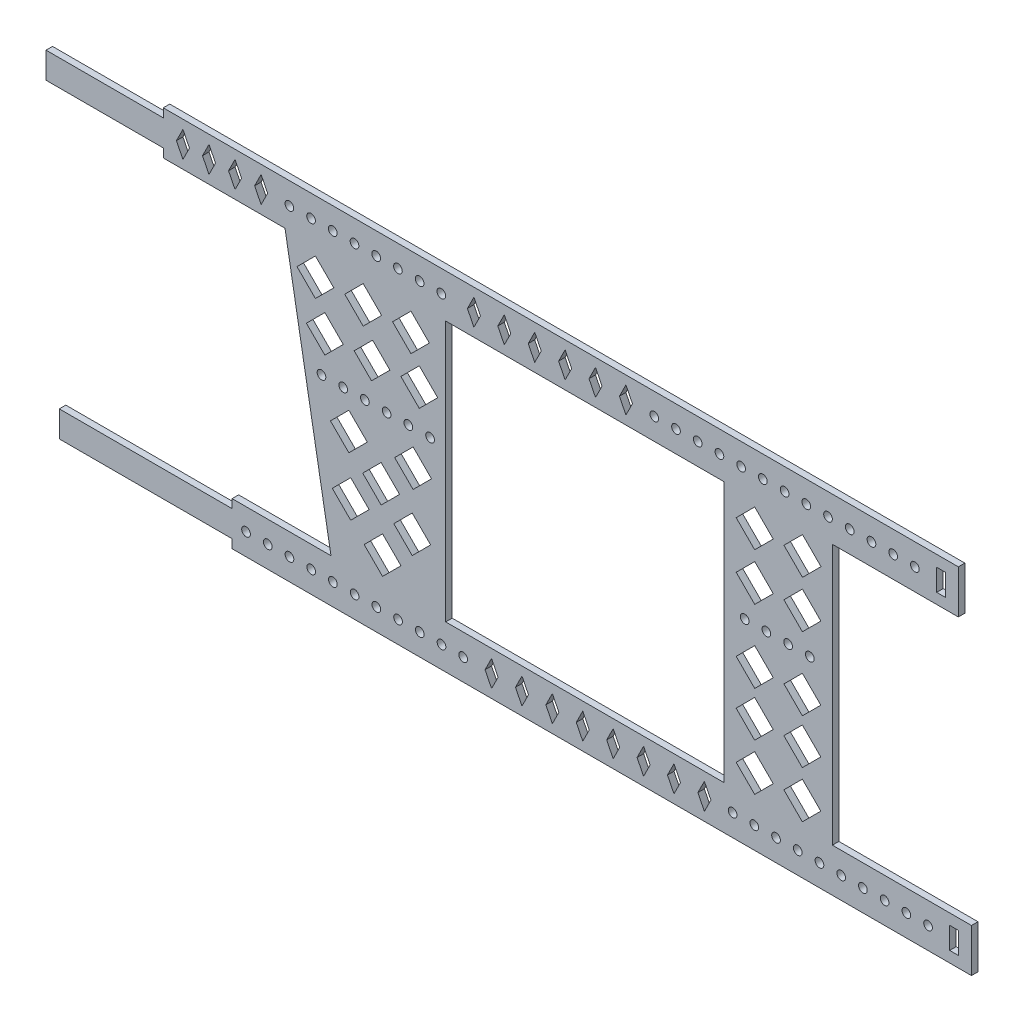
SolidWorks part; units mm, degrees
ref_plane "前视基准面" through (0, 0, 0) normal (0, 0, 1) x (1, 0, 0)
ref_plane "上视基准面" through (0, 0, 0) normal (0, 1, 0) x (1, 0, 0)
ref_plane "右视基准面" through (0, 0, 0) normal (1, 0, 0) x (0, 0, -1)
other "Configuration Table"
sketch "草图1" plane through (0, 0, 0) normal (0, 0, 1) x (1, 0, 0)
  line L4 (-82, 0.0001) -> (-80.5, 3.0002)
  line L11 (0, 0) -> (121.948, 0) construction
  line L17 (-82, 0.0001) -> (-80.4999, -3.0001)
  line L18 (-80.5, 3.0002) -> (-78.9999, 0)
  line L44 (-80.4999, -3.0001) -> (-78.9999, 0)
  line L49 (-76, 0.0001) -> (-74.5, 3.0002)
  line L51 (-91.0305, 5.0353) -> (88.0306, 5.0353)
  line L53 (-91.0305, -4.9647) -> (-62.9999, -4.9647)
  line L66 (-85, 0.0003) -> (-85, -0.0003)
  line L72 (-76, 0.0001) -> (-74.4999, -3.0001)
  line L73 (-62.9999, -4.9647) -> (-52.4203, -64.9647)
  line L74 (63.0306, -4.9647) -> (88.0306, -4.9647)
  line L75 (-25.9999, -4.9647) -> (-25.9999, -64.9647)
  line L77 (-74.4999, -3.0001) -> (-72.9999, 0)
  line L78 (-74.5, 3.0002) -> (-72.9999, 0)
  line L79 (-70, 0.0001) -> (-68.5, 3.0002)
  line L80 (-70, 0.0001) -> (-68.4999, -3.0001)
  line L81 (-68.4999, -3.0001) -> (-66.9999, 0)
  line L82 (-68.5, 3.0002) -> (-66.9999, 0)
  line L83 (-61.9999, 0) -> (-56.9999, 0) construction
  line L84 (-62.9999, 0) -> (-62.9999, -4.9647) construction
  line L85 (-25.9999, 0) -> (-25.9999, -8.8507) construction
  line L86 (-21, 0.04) -> (-19.5, 3.04)
  line L87 (-21, 0.04) -> (-19.5, -2.96)
  line L88 (-19.5, -2.96) -> (-18, 0.04)
  line L89 (-19.5, 3.04) -> (-18, 0.04)
  line L90 (-14, 0.04) -> (-12.5, 3.04)
  line L91 (-12.5, 3.04) -> (-11, 0.04)
  line L92 (-12.5, -2.96) -> (-11, 0.04)
  line L93 (-14, 0.04) -> (-12.5, -2.96)
  line L94 (-7, 0.04) -> (-5.5, 3.04)
  line L95 (-5.5, 3.04) -> (-4, 0.04)
  line L96 (-5.5, -2.96) -> (-4, 0.04)
  line L97 (-7, 0.04) -> (-5.5, -2.96)
  line L98 (0, 0.04) -> (1.5, 3.04)
  line L99 (1.5, 3.04) -> (3, 0.04)
  line L100 (1.5, -2.96) -> (3, 0.04)
  line L101 (0, 0.04) -> (1.5, -2.96)
  line L102 (7, 0.04) -> (8.5, 3.04)
  line L103 (8.5, 3.04) -> (10, 0.04)
  line L104 (8.5, -2.96) -> (10, 0.04)
  line L105 (7, 0.04) -> (8.5, -2.96)
  line L106 (14, 0.04) -> (15.5, 3.04)
  line L107 (15.5, 3.04) -> (17, 0.04)
  line L108 (15.5, -2.96) -> (17, 0.04)
  line L109 (14, 0.04) -> (15.5, -2.96)
  line L110 (-21, 0.04) -> (-14, 0.04) construction
  line L111 (22.0306, 0.0331) -> (27.0306, 0.0331) construction
  line L117 (38.0306, 0.0331) -> (38.0306, -8.8507) construction
  line L118 (63.0306, 0.0331) -> (63.0306, 0) construction
  line L138 (-55.9986, -6.9922) -> (-60.2412, -11.2349)
  line L143 (-44.9986, -6.9922) -> (-49.2412, -11.2349)
  line L144 (-44.9986, -6.9922) -> (-40.7559, -11.2349)
  line L145 (-55.9986, -6.9922) -> (-51.7559, -11.2349)
  line L146 (-60.2412, -11.2349) -> (-55.9986, -15.4775)
  line L147 (-51.7559, -11.2349) -> (-55.9986, -15.4775)
  line L148 (-40.7559, -11.2349) -> (-44.9986, -15.4775)
  line L149 (-49.2412, -11.2349) -> (-44.9986, -15.4775)
  line L150 (-33.9986, -6.9922) -> (-38.2412, -11.2349)
  line L151 (-33.9986, -6.9922) -> (-29.7559, -11.2349)
  line L152 (-29.7559, -11.2349) -> (-33.9986, -15.4775)
  line L153 (-38.2412, -11.2349) -> (-33.9986, -15.4775)
  line L154 (-55.9986, -6.9922) -> (-44.9986, -6.9922) construction
  line L167 (-53.8279, -17.1935) -> (-58.0705, -21.4361)
  line L168 (-42.8279, -17.1935) -> (-47.0705, -21.4361)
  line L169 (-42.8279, -17.1935) -> (-38.8399, -21.1815)
  line L170 (-53.8279, -17.1935) -> (-49.5852, -21.4361)
  line L171 (-58.0705, -21.4361) -> (-53.8279, -25.6788)
  line L172 (-49.5852, -21.4361) -> (-53.8279, -25.6788)
  line L173 (-38.8399, -21.1815) -> (-43.0826, -25.4241)
  line L174 (-47.0705, -21.4361) -> (-43.0826, -25.4241)
  line L175 (-32.0826, -16.9388) -> (-36.3252, -21.1815)
  line L176 (-32.0826, -16.9388) -> (-27.8399, -21.1815)
  line L177 (-27.8399, -21.1815) -> (-32.0826, -25.4241)
  line L178 (-36.3252, -21.1815) -> (-32.0826, -25.4241)
  line L179 (-53.8279, -17.1935) -> (-42.8279, -17.1935) construction
  line L180 (63.0306, -29.9647) -> (-66.6645, -29.9647) construction
  line L181 (-54.5983, -30) -> (-49.5983, -30) construction
  line L186 (-48.294, -33.8993) -> (-52.5367, -38.1419)
  line L187 (-52.5367, -38.1419) -> (-48.294, -42.3846)
  line L188 (-44.0514, -38.1419) -> (-48.294, -42.3846)
  line L189 (-48.294, -33.8993) -> (-44.0514, -38.1419)
  line L190 (-33.5054, -33.8232) -> (-37.7481, -38.0658)
  line L191 (-37.7481, -38.0658) -> (-33.5054, -42.3084)
  line L192 (-29.2628, -38.0658) -> (-33.5054, -42.3084)
  line L193 (-33.5054, -33.8232) -> (-29.2628, -38.0658)
  line L195 (-47.8719, -47.1411) -> (-52.1146, -51.3837)
  line L196 (-52.1146, -51.3837) -> (-47.8719, -55.6263)
  line L197 (-43.6293, -51.3837) -> (-47.8719, -55.6263)
  line L198 (-47.8719, -47.1411) -> (-43.6293, -51.3837)
  line L199 (-40.8637, -40.6049) -> (-45.1063, -44.8475)
  line L200 (-45.1063, -44.8475) -> (-40.8637, -49.0901)
  line L201 (-36.6211, -44.8475) -> (-40.8637, -49.0901)
  line L202 (-40.8637, -40.6049) -> (-36.6211, -44.8475)
  line L203 (-40.5381, -54.6754) -> (-44.7807, -58.9181)
  line L204 (-44.7807, -58.9181) -> (-40.5381, -63.1607)
  line L205 (-36.2954, -58.9181) -> (-40.5381, -63.1607)
  line L206 (-40.5381, -54.6754) -> (-36.2954, -58.9181)
  line L207 (-33.7086, -47.1027) -> (-37.9513, -51.3454)
  line L208 (-37.9513, -51.3454) -> (-33.7086, -55.588)
  line L209 (-29.466, -51.3454) -> (-33.7086, -55.588)
  line L210 (-33.7086, -47.1027) -> (-29.466, -51.3454)
  line L215 (-52.4203, -64.9647) -> (-75.171, -64.9647)
  line L216 (-25.9999, -64.9647) -> (38.0306, -64.9647)
  line L217 (38.0306, -4.9647) -> (38.0306, -64.9647)
  line L218 (63.0306, -4.9647) -> (63.0306, -64.9647)
  line L219 (42.8446, -29.9642) -> (47.8446, -29.9642) construction
  line L220 (45.1493, -6.4688) -> (40.8811, -10.737)
  line L221 (40.8811, -10.737) -> (45.1493, -15.0051)
  line L222 (49.4174, -10.737) -> (45.1493, -15.0051)
  line L223 (45.1493, -6.4688) -> (49.4174, -10.737)
  line L224 (56.1493, -6.4688) -> (51.8811, -10.737)
  line L225 (51.8811, -10.737) -> (56.1493, -15.0051)
  line L226 (60.4174, -10.737) -> (56.1493, -15.0051)
  line L227 (56.1493, -6.4688) -> (60.4174, -10.737)
  line L228 (45.1493, -6.4688) -> (56.1493, -6.4688) construction
  line L229 (45.1571, -17.3518) -> (40.889, -21.62)
  line L230 (40.889, -21.62) -> (45.1571, -25.8881)
  line L231 (49.4253, -21.62) -> (45.1571, -25.8881)
  line L232 (45.1571, -17.3518) -> (49.4253, -21.62)
  line L233 (56.1316, -17.3518) -> (51.8762, -21.6072)
  line L234 (51.8762, -21.6072) -> (56.1316, -25.8626)
  line L235 (60.387, -21.6072) -> (56.1316, -25.8626)
  line L236 (56.1316, -17.3518) -> (60.387, -21.6072)
  line L237 (45.1571, -17.3518) -> (56.1316, -17.3518) construction
  line L238 (45.1553, -34.115) -> (40.8872, -38.3832)
  line L239 (40.8872, -38.3832) -> (45.1553, -42.6513)
  line L240 (49.4235, -38.3832) -> (45.1553, -42.6513)
  line L241 (45.1553, -34.115) -> (49.4235, -38.3832)
  line L242 (56.1298, -34.1405) -> (51.8872, -38.3832)
  line L243 (51.8872, -38.3832) -> (56.1298, -42.6258)
  line L244 (60.3725, -38.3832) -> (56.1298, -42.6258)
  line L245 (56.1298, -34.1405) -> (60.3725, -38.3832)
  line L246 (45.1553, -34.115) -> (56.1298, -34.1405) construction
  line L247 (45.142, -44.4521) -> (40.8738, -48.7203)
  line L248 (40.8738, -48.7203) -> (45.142, -52.9884)
  line L249 (49.4101, -48.7203) -> (45.142, -52.9884)
  line L250 (45.142, -44.4521) -> (49.4101, -48.7203)
  line L251 (56.1165, -44.4521) -> (51.8611, -48.7075)
  line L252 (51.8611, -48.7075) -> (56.1165, -52.9629)
  line L253 (60.3719, -48.7075) -> (56.1165, -52.9629)
  line L254 (56.1165, -44.4521) -> (60.3719, -48.7075)
  line L255 (45.142, -44.4521) -> (56.1165, -44.4521) construction
  line L256 (45.146, -55.2548) -> (40.8778, -59.523)
  line L257 (40.8778, -59.523) -> (45.146, -63.7911)
  line L258 (49.4141, -59.523) -> (45.146, -63.7911)
  line L259 (45.146, -55.2548) -> (49.4141, -59.523)
  line L260 (56.1205, -55.2548) -> (51.8651, -59.5102)
  line L261 (51.8651, -59.5102) -> (56.1205, -63.7656)
  line L262 (60.3759, -59.5102) -> (56.1205, -63.7656)
  line L263 (56.1205, -55.2548) -> (60.3759, -59.5102)
  line L264 (45.146, -55.2548) -> (56.1205, -55.2548) construction
  line L265 (45.1493, -6.4943) -> (45.1493, -76.2288) construction
  line L266 (0, 0.04) -> (0, -21.1815) construction
  line L267 (-87.9694, -66.9647) -> (-114.9694, -66.9647)
  line L268 (-75.171, -74.9647) -> (88.0306, -74.9647)
  line L269 (63.0306, -64.9647) -> (88.0306, -64.9647)
  line L270 (88.0306, -64.9647) -> (95.0646, -64.9647)
  line L271 (95.0646, -64.9647) -> (95.0646, -74.9647)
  line L272 (-87.9694, -66.9647) -> (-75.171, -66.9647)
  line L273 (88.0306, -74.9647) -> (95.0646, -74.9647)
  line L274 (-75.171, -66.9647) -> (-75.171, -64.9647)
  line L276 (47.8446, -29.9642) -> (52.8446, -29.9642) construction
  line L277 (52.8446, -29.9642) -> (50.3446, -29.9642) construction
  line L278 (50.3446, -29.9642) -> (50.3446, -32.9055) construction
  line L279 (40.0646, -69.9647) -> (45.0646, -69.9647) construction
  line L287 (-114.9694, -66.9647) -> (-114.9694, -72.9647)
  line L288 (-114.9694, -72.9647) -> (-87.9694, -72.9647)
  line L311 (90.0414, -67.4468) -> (92.0414, -67.4468)
  line L312 (-90.9389, -69.9647) -> (-66.4869, -69.9647) construction
  line L313 (-71.9694, -69.9647) -> (-66.9694, -69.9647) construction
  line L314 (-16.9354, -69.9662) -> (-15.4354, -66.9662)
  line L315 (-15.4354, -66.9662) -> (-13.9354, -69.9662)
  line L316 (-15.4354, -72.9662) -> (-13.9354, -69.9662)
  line L317 (-16.9354, -69.9662) -> (-15.4354, -72.9662)
  line L318 (-9.9354, -69.9662) -> (-8.4354, -66.9662)
  line L319 (-8.4354, -66.9662) -> (-6.9354, -69.9662)
  line L320 (-8.4354, -72.9662) -> (-6.9354, -69.9662)
  line L321 (-9.9354, -69.9662) -> (-8.4354, -72.9662)
  line L322 (-2.9354, -69.9662) -> (-1.4354, -66.9662)
  line L323 (-1.4354, -66.9662) -> (0.0646, -69.9662)
  line L324 (-1.4354, -72.9662) -> (0.0646, -69.9662)
  line L325 (-2.9354, -69.9662) -> (-1.4354, -72.9662)
  line L326 (4.0646, -69.9662) -> (5.5646, -66.9662)
  line L327 (5.5646, -66.9662) -> (7.0646, -69.9662)
  line L328 (5.5646, -72.9662) -> (7.0646, -69.9662)
  line L329 (4.0646, -69.9662) -> (5.5646, -72.9662)
  line L330 (11.0646, -69.9662) -> (12.5646, -66.9662)
  line L331 (12.5646, -66.9662) -> (14.0646, -69.9662)
  line L332 (12.5646, -72.9662) -> (14.0646, -69.9662)
  line L333 (11.0646, -69.9662) -> (12.5646, -72.9662)
  line L334 (18.0646, -69.9662) -> (19.5646, -66.9662)
  line L335 (19.5646, -66.9662) -> (21.0646, -69.9662)
  line L336 (19.5646, -72.9662) -> (21.0646, -69.9662)
  line L337 (18.0646, -69.9662) -> (19.5646, -72.9662)
  line L338 (25.0646, -69.9662) -> (26.5646, -66.9662)
  line L339 (26.5646, -66.9662) -> (28.0646, -69.9662)
  line L340 (26.5646, -72.9662) -> (28.0646, -69.9662)
  line L341 (25.0646, -69.9662) -> (26.5646, -72.9662)
  line L342 (32.0646, -69.9662) -> (33.5646, -66.9662)
  line L343 (33.5646, -66.9662) -> (35.0646, -69.9662)
  line L344 (33.5646, -72.9662) -> (35.0646, -69.9662)
  line L345 (32.0646, -69.9662) -> (33.5646, -72.9662)
  line L346 (-16.9354, -69.9662) -> (-9.9354, -69.9662) construction
  line L350 (63.0306, -4.9647) -> (63.0306, -8.8507) construction
  line L351 (87.048, 2.4576) -> (87.048, -2.5424)
  line L352 (87.048, 2.4576) -> (89.048, 2.4576)
  line L353 (89.048, 2.4576) -> (89.048, -2.5424)
  line L354 (87.048, -2.5424) -> (89.048, -2.5424)
  line L355 (88.0306, 5.0353) -> (92.0306, 5.0353)
  line L356 (92.0306, 5.0353) -> (92.0306, -4.9647)
  line L357 (92.0306, -4.9647) -> (88.0306, -4.9647)
  line L361 (-93.1206, 3.0353) -> (-118.0305, 3.0353)
  line L363 (-88, 0.0001) -> (-86.5, 3.0002)
  line L364 (-88, 0.0001) -> (-86.4999, -3.0001)
  line L365 (-86.5, 3.0002) -> (-84.9999, 0)
  line L366 (-86.4999, -3.0001) -> (-84.9999, 0)
  line L371 (-118.0305, 3.0353) -> (-118.0305, -2.9647)
  line L372 (-94, 0.0001) -> (-92.5, 3.0002) [skipped]
  line L373 (-92.5, 3.0002) -> (-90.9999, 0) [skipped]
  line L374 (-92.4999, -3.0001) -> (-90.9999, 0) [skipped]
  line L375 (-94, 0.0001) -> (-92.4999, -3.0001) [skipped]
  line L376 (-92.6838, -2.9647) -> (-118.0305, -2.9647)
  line L377 (-91.0305, 5.0353) -> (-91.0305, 3.0353)
  line L378 (-91.0305, 3.0353) -> (-93.1206, 3.0353)
  line L379 (-75.171, -72.9647) -> (-75.171, -74.9647)
  line L380 (-92.6838, -2.9647) -> (-91.0305, -2.9647)
  line L381 (-91.0305, -2.9647) -> (-91.0305, -4.9647)
  line L382 (-25.9999, -4.9647) -> (38.0306, -4.9647)
  line L383 (92.0414, -67.4468) -> (92.0414, -72.4468)
  line L384 (90.0414, -72.4468) -> (92.0414, -72.4468)
  line L385 (90.0414, -67.4468) -> (90.0414, -72.4468)
  line L387 (-87.9694, -72.9647) -> (-75.171, -72.9647)
  circle A0 centre (-61.9999, 0) radius 1
  circle A1 centre (-56.9999, 0) radius 1
  circle A2 centre (-51.9999, 0) radius 1
  circle A3 centre (-46.9999, 0) radius 1
  circle A4 centre (-41.9999, 0) radius 1
  circle A5 centre (-36.9999, 0) radius 1
  circle A6 centre (-31.9999, 0) radius 1
  circle A7 centre (-26.9999, 0) radius 1
  circle A8 centre (22.0306, 0.0331) radius 1
  circle A9 centre (27.0306, 0.0331) radius 1
  circle A10 centre (32.0306, 0.0331) radius 1
  circle A11 centre (37.0306, 0.0331) radius 1
  circle A12 centre (42.0306, 0.0331) radius 1
  circle A13 centre (47.0306, 0.0331) radius 1
  circle A14 centre (52.0306, 0.0331) radius 1
  circle A15 centre (57.0306, 0.0331) radius 1
  circle A16 centre (62.0306, 0.0331) radius 1
  circle A17 centre (67.0306, 0.0331) radius 1
  circle A18 centre (72.0306, 0.0331) radius 1
  circle A19 centre (77.0306, 0.0331) radius 1
  circle A20 centre (82.0306, 0.0331) radius 1
  circle A21 centre (-55.9986, -11.2349) radius 4.2426 construction
  circle A23 centre (-53.8279, -21.4361) radius 4.2426 construction
  circle A24 centre (-54.5983, -30) radius 1
  circle A25 centre (-49.5983, -30) radius 1
  circle A26 centre (-44.5983, -30) radius 1
  circle A27 centre (-39.5983, -30) radius 1
  circle A28 centre (-34.5983, -30) radius 1
  circle A29 centre (-29.5983, -30) radius 1
  circle A30 centre (42.8446, -29.9642) radius 1
  circle A31 centre (47.8446, -29.9642) radius 1
  circle A32 centre (52.8446, -29.9642) radius 1
  circle A33 centre (57.8446, -29.9642) radius 1
  circle A38 centre (-71.9694, -69.9647) radius 1
  circle A39 centre (-66.9694, -69.9647) radius 1
  circle A40 centre (-61.9694, -69.9647) radius 1
  circle A41 centre (-56.9694, -69.9647) radius 1
  circle A42 centre (-51.9694, -69.9647) radius 1
  circle A43 centre (-46.9694, -69.9647) radius 1
  circle A44 centre (-41.9694, -69.9647) radius 1
  circle A45 centre (-36.9694, -69.9647) radius 1
  circle A46 centre (-31.9694, -69.9647) radius 1
  circle A47 centre (-26.9694, -69.9647) radius 1
  circle A48 centre (-21.9694, -69.9647) radius 1
  circle A50 centre (-16.9694, -69.9647) radius 1 [skipped]
  circle A51 centre (40.0646, -69.9647) radius 1
  circle A52 centre (45.0646, -69.9647) radius 1
  circle A53 centre (50.0646, -69.9647) radius 1
  circle A54 centre (55.0646, -69.9647) radius 1
  circle A55 centre (60.0646, -69.9647) radius 1
  circle A56 centre (65.0646, -69.9647) radius 1
  circle A57 centre (70.0646, -69.9647) radius 1
  circle A58 centre (75.0646, -69.9647) radius 1
  circle A59 centre (80.0646, -69.9647) radius 1
  circle A60 centre (85.0646, -69.9647) radius 1
  point P0 (0, 0)
  point P11 (-61.9999, 0)
  point P32 (0, 0)
  point P33 (-96, 0)
  point P35 (0, 0)
  point P41 (-96, 0)
  point P44 (-88, 0.0001)
  point P46 (-82, 0.0001)
  point P60 (-20.9999, 0)
  point P74 (22, 0)
  point P100 (88.0306, 0)
  point P128 (88.0306, -3)
  point P129 (88.0306, 3)
  point P130 (88.0306, 0)
  point P133 (88.0306, 5.0353)
  point P135 (89.375, -69.9647)
  point P136 (88.0306, -4.9647)
  point P169 (-25.9999, -29.9647)
  point P172 (-54.5983, -29.9647)
  point P175 (-99.9999, 3.0353)
  point P188 (-99.5631, -2.9647)
  point P200 (91.0646, -69.9647)
  point P201 (90.3686, -69.9647)
  point P220 (63.0306, -4.9647)
  point P225 (42.8454, -29.9647)
  point P291 (88.0306, -64.9647)
  point P307 (40.0646, -69.9647)
  point P310 (95.0646, -69.9647)
  point P319 (-87.9694, -69.9775)
  point P320 (-87.9694, -69.9775)
  point P332 (-71.9694, -69.9647)
  point P416 (-94, 0.0001)
  dimension "D7" = 2
  dimension "D32" = 8.4853
  dimension "D34" = 8.4853
  dimension "D43" = 11
  dimension "D58" = 2
  dimension "D64" = 2
  dimension "D4" = 3
  dimension "D8" = 5
  dimension "D9" = 183.0611
  dimension "D10" = 39.7984
  dimension "D11" = 3
  dimension "D12" = 170.2356
  dimension "D13" = 6
  dimension "D15" = 8
  dimension "D6" = 5
  dimension "D16" = 5
  dimension "D18" = 7
  dimension "D19" = 5
  dimension "D20" = 5
  dimension "D21" = 6
  dimension "D22" = 6
  dimension "D23" = 4
  dimension "D24" = 27
  dimension "D28" = 100
  dimension "D29" = 60
  dimension "D30" = 11
  dimension "D31" = 3
  dimension "D33" = 6
  dimension "D35" = 6
  dimension "D36" = 5
  dimension "D37" = 25
  dimension "D38" = 6
  dimension "D41" = 5
  dimension "D44" = 2
  dimension "D42" = 60
  dimension "D59" = 5
  dimension "D61" = 12
  dimension "D62" = 7
  dimension "D63" = 5
  dimension "D65" = 5
  dimension "D67" = 4
  dimension "D17" = 3
  dimension "D60" = 6
  dimension "D27" = 13
  dimension "D51" = 4
extrude "凸台-拉伸1" add sketch "草图1" along normal blind 1.5 contours L288 L387 L379 L268 L273 L271 L270 L269 L218 L74 L357 L356 L355 L51 L377 L378 L361 L371 L376 L380 L381 L53 L73 L215 L274 L272 L267 L287 A60 A59 A58 A57 A56 A55 A54 A53 A52 A51 A48
